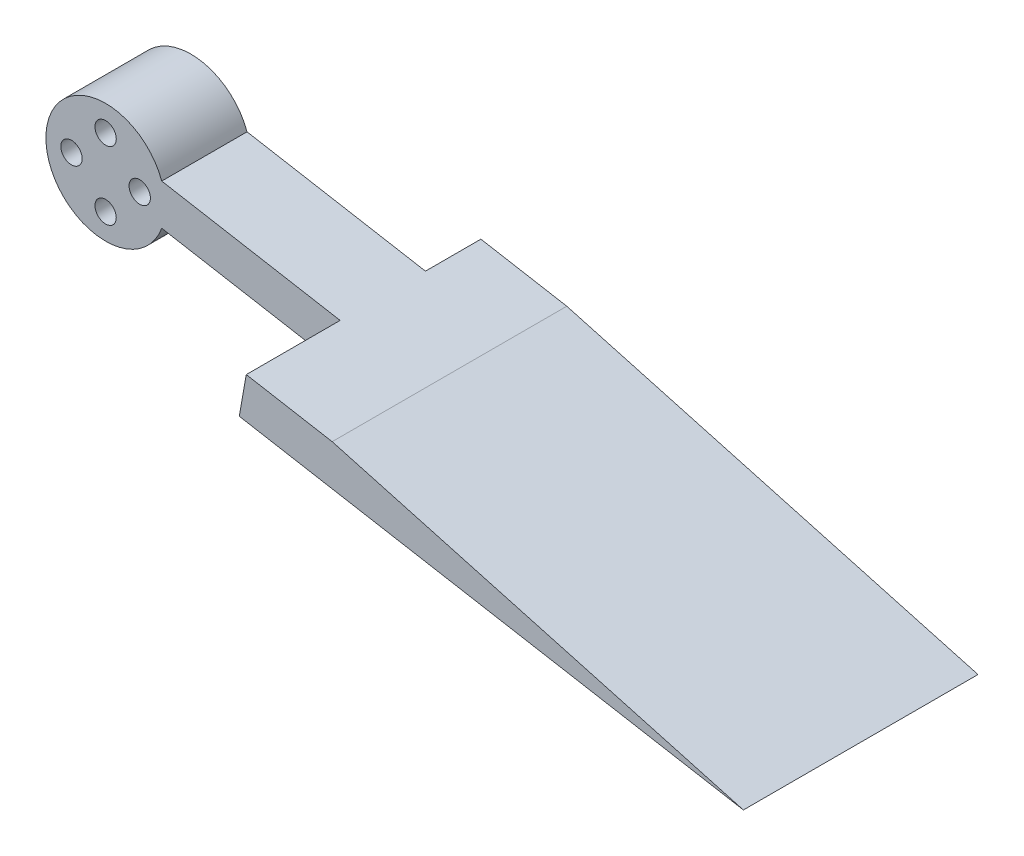
SolidWorks part; units mm, degrees
ref_plane "정면" through (0, 0, 0) normal (0, 0, 1) x (1, 0, 0)
ref_plane "윗면" through (0, 0, 0) normal (0, 1, 0) x (1, 0, 0)
ref_plane "우측면" through (0, 0, 0) normal (1, 0, 0) x (0, 0, -1)
sketch "스케치1" plane through (0, 0, 0) normal (0, 0, 1) x (1, 0, 0)
  line L0 (0, 0) -> (14.5053, 0) construction
  line L1 (0, 0) -> (13.7572, 5.0072) construction
  line L2 (0, 0) -> (14.0337, -5.1078) construction
  line L3 (6.5778, 2.3941) -> (86.5778, -11.712)
  line L4 (86.5778, -11.712) -> (85.759, -16.3559)
  line L5 (85.759, -16.3559) -> (6.5778, -2.3941)
  arc A0 (6.5778, 2.3941) -> (6.5778, -2.3941) centre (0, 0) ccw
  dimension "D1" = 14
  dimension "D2" = 20
  dimension "D3" = 20
  dimension "D4" = 10
  dimension "D5" = 80
extrude "보스-돌출1" add sketch "스케치1" along normal blind 10
sketch "스케치2" plane through (0, 0, 10) normal (0, 0, 1) x (1, 0, 0)
  line L0 (86.5778, -11.712) -> (27.4894, -1.2931)
  line L1 (86.5778, -11.712) -> (6.5778, 2.3941) construction
  line L2 (27.4894, -1.2931) -> (26.6705, -5.937)
  line L3 (6.5778, -2.3941) -> (85.759, -16.3559) construction
  line L4 (26.6705, -5.937) -> (85.759, -16.3559)
  line L5 (85.759, -16.3559) -> (86.5778, -11.712)
  dimension "D1" = 60
extrude "보스-돌출2" add sketch "스케치2" along normal blind 11 and the other way blind 16.5
sketch "스케치4" plane through (0, 0, 21) normal (0, 0, 1) x (1, 0, 0)
  line L0 (86.5778, -11.712) -> (85.759, -16.3559)
  line L1 (85.759, -16.3559) -> (37.5569, -3.0683)
  line L2 (86.5778, -11.712) -> (27.4894, -1.2931) construction
  line L3 (37.5569, -3.0683) -> (86.5778, -11.712)
  dimension "D1" = 50
extrude "컷-돌출1" cut sketch "스케치4" against normal through all
hole_wizard "M3 나사 구멍1" positions "스케치5" profile "스케치6" tap size "M3" standard "ISO" end condition through all
sketch "스케치5" plane through (0, 0, 10) normal (0, 0, 1) x (1, 0, 0)
  circle A0 centre (0, 0) radius 4 construction
  point P5 (0, 4)
  point P7 (4, 0)
  point P9 (0, -4)
  point P11 (-4, 0)
  dimension "D1" = 8
sketch "스케치6" plane through (-4, 0, 10) normal (1, 0, 0) x (0, -1, 0)
  line L0 (0, 0) -> (0, 16.5)
  line L1 (0, 16.5) -> (1.25, 16.5)
  line L2 (1.25, 16.5) -> (1.25, 0)
  line L5 (1.25, 0) -> (0, 0)
  line L11 (0, -6.35) -> (0, 107.95) construction
  dimension "관통 탭 드릴 지름" = 2.5
  dimension "관통 탭 드릴 깊이" = 16.5
cosmetic thread "구멍 나사산1" parameters "D2"=3
cosmetic thread "구멍 나사산2" parameters "D2"=3
cosmetic thread "구멍 나사산3" parameters "D2"=3
cosmetic thread "구멍 나사산4" parameters "D2"=3
